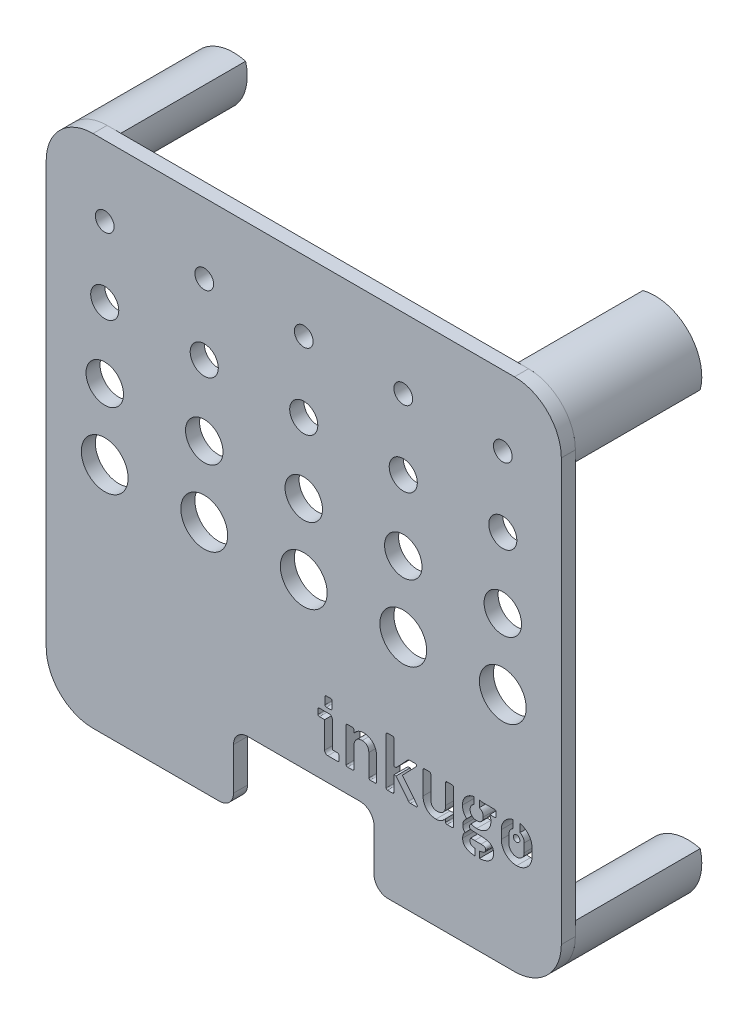
SolidWorks part; units mm, degrees
ref_plane "Front Plane" through (0, 0, 0) normal (0, 0, 1) x (1, 0, 0)
ref_plane "Top Plane" through (0, 0, 0) normal (0, 1, 0) x (1, 0, 0)
ref_plane "Right Plane" through (0, 0, 0) normal (1, 0, 0) x (0, 0, -1)
sketch "Sketch1" plane through (0, 0, 0) normal (0, 0, 1) x (1, 0, 0)
  line L1 (0, 0) -> (110, 0)
  line L2 (0, 0) -> (0, 110)
  line L3 (0, 110) -> (110, 110)
  line L4 (110, 0) -> (110, 110)
  dimension "D1" = 110
  dimension "D2" = 110
extrude "Boss-Extrude1" add sketch "Sketch1" along normal blind 3
fillet "Fillet1" radius 10 4 edges at (0, 0, 1.5) (110, 0, 1.5) (110, 110, 1.5) (0, 110, 1.5)
sketch "Sketch4" plane through (0, 0, 3) normal (0, 0, 1) x (1, 0, 0)
  line L0 (57.5, 115.8667) -> (57.5, 0.8667) construction
  line L1 (110, 20) -> (57.5, 20) construction
  line L3 (0, 57.5) -> (115, 57.5) construction
  line L5 (110, 10) -> (110, 100) construction
  line L6 (100, 110) -> (10, 110) construction
  line L7 (0, 100) -> (0, 10) construction
  line L8 (10, 0) -> (100, 0) construction
  circle A0 centre (12.5, 95) radius 2
  circle A1 centre (33.75, 95) radius 2
  circle A2 centre (55, 95) radius 2
  circle A3 centre (76.25, 95) radius 2
  circle A4 centre (97.5, 95) radius 2
  circle A5 centre (12.5, 80) radius 3
  circle A6 centre (33.75, 80) radius 3
  circle A7 centre (55, 80) radius 3
  circle A8 centre (76.25, 80) radius 3
  circle A9 centre (97.5, 80) radius 3
  circle A10 centre (12.5, 65) radius 4
  circle A11 centre (33.75, 65) radius 4
  circle A12 centre (55, 65) radius 4
  circle A13 centre (76.25, 65) radius 4
  circle A14 centre (97.5, 65) radius 4
  circle A15 centre (12.5, 50) radius 5
  circle A16 centre (33.75, 50) radius 5
  circle A17 centre (55, 50) radius 5
  circle A18 centre (76.25, 50) radius 5
  circle A19 centre (97.5, 50) radius 5
  text T0 "<b>inkugo</b>" font "Miriam Libre" height in points 28
  dimension "D1" = 4
  dimension "D2" = 15
  dimension "D3" = 12.5
  dimension "D5" = 6
  dimension "D6" = 15
  dimension "D7" = 5
  dimension "D8" = 15
  dimension "D10" = 15
  dimension "D4" = 5
  dimension "D12" = 20
  dimension "D9" = 5
  dimension "D11" = 5
extrude "Cut-Extrude1" cut sketch "Sketch4" against normal blind 27
sketch "Sketch8" plane through (0, 0, 0) normal (0, 0, -1) x (-1, 0, 0)
  circle A0 centre (-100, 100) radius 10
  circle A1 centre (-107.0711, 107.0711) radius 10
  arc A2 (-100, 110) -> (-110, 100) centre (-100, 100) ccw construction
  circle A3 centre (-10, 100) radius 10
  circle A4 centre (-2.9289, 107.0711) radius 10
  arc A5 (0, 100) -> (-10, 110) centre (-10, 100) ccw construction
  circle A6 centre (-107.0711, 2.9289) radius 10
  arc A7 (-110, 10) -> (-100, 0) centre (-100, 10) ccw construction
  circle A8 centre (-100, 10) radius 10
  circle A9 centre (-2.9289, 2.9289) radius 10
  arc A10 (-10, 0) -> (0, 10) centre (-10, 10) ccw construction
  circle A11 centre (-10, 10) radius 10
extrude "Boss-Extrude5" add sketch "Sketch8" along normal blind 27 contours A0 A1 | A3 A4 | A9 A11 | A6 A8
sketch "Sketch9" plane through (0, 0, 3) normal (0, 0, 1) x (1, 0, 0)
  line L0 (10, 0) -> (100, 0) construction
  line L1 (70, 0) -> (40, 0)
  line L2 (70, 0) -> (70, 15)
  line L3 (70, 15) -> (40, 15)
  line L4 (40, 0) -> (40, 15)
  line L5 (110, 10) -> (110, 100) construction
  dimension "D1" = 30
  dimension "D2" = 40
  dimension "D3" = 15
extrude "Cut-Extrude5" cut sketch "Sketch9" against normal blind 27
fillet "Fillet2" radius 3 4 edges at (40, 15, 1.5) (70, 15, 1.5) (70, 0, 1.5) (40, 0, 1.5)
sketch "Sketch10" plane through (0, 0, 3) normal (0, 0, 1) x (1, 0, 0)
  line L0 (102.0803, 23.0444) -> (102.0803, 24.8475) construction
  line L1 (91.3872, 28.6939) -> (92.4818, 28.6939)
  line L2 (91.3872, 28.6939) -> (91.3872, 26.2486)
  line L3 (91.3872, 26.2486) -> (92.4818, 26.2486)
  line L4 (92.4818, 28.6939) -> (92.4818, 26.2486)
  line L5 (91.5735, 18.7961) -> (92.4818, 18.7961)
  line L6 (91.5735, 18.7961) -> (91.5735, 16.7466)
  line L7 (91.5735, 16.7466) -> (92.4818, 16.7466)
  line L8 (92.4818, 18.7961) -> (92.4818, 16.7466)
  line L13 (99.7113, 29.0401) -> (101.1903, 29.0401)
  line L14 (99.7113, 29.0401) -> (99.7113, 26.3033)
  line L15 (99.7113, 26.3033) -> (101.1903, 26.3033)
  line L16 (101.1903, 29.0401) -> (101.1903, 26.3033)
  spline S0 degree 3 poles (102.0803, 24.8475) (102.0786, 24.9027) (102.0753, 25.0116) (102.0535, 25.1719) (102.015, 25.3258) (101.9636, 25.4736) (101.8966, 25.615) (101.8155, 25.7506) (101.7164, 25.8782) (101.6058, 25.9989) (101.4851, 26.1095) (101.3576, 26.2086) (101.2219, 26.2897) (101.0805, 26.3567) (100.9328, 26.408) (100.7789, 26.4465) (100.6185, 26.4684) (100.5097, 26.4717) (100.4545, 26.4734) knots 0 0 0 0 0.064737 0.127649 0.189436 0.250541 0.310832 0.372693 0.435488 0.5 0.564512 0.627307 0.689168 0.749459 0.810564 0.872351 0.935263 1 1 1 1 construction
  dimension "D1" = 0.89
extrude "Boss-Extrude6" add sketch "Sketch10" against normal blind 3
sketch "Sketch12" plane through (0, 0, 3) normal (0, 0, 1) x (1, 0, 0)
  line L0 (102.0803, 23.0444) -> (102.0803, 24.8475) construction
  circle A0 centre (100.4503, 24.8475) radius 0.7
  dimension "D1" = 1.63
extrude "Cut-Extrude6" cut sketch "Sketch12" against normal blind 3
